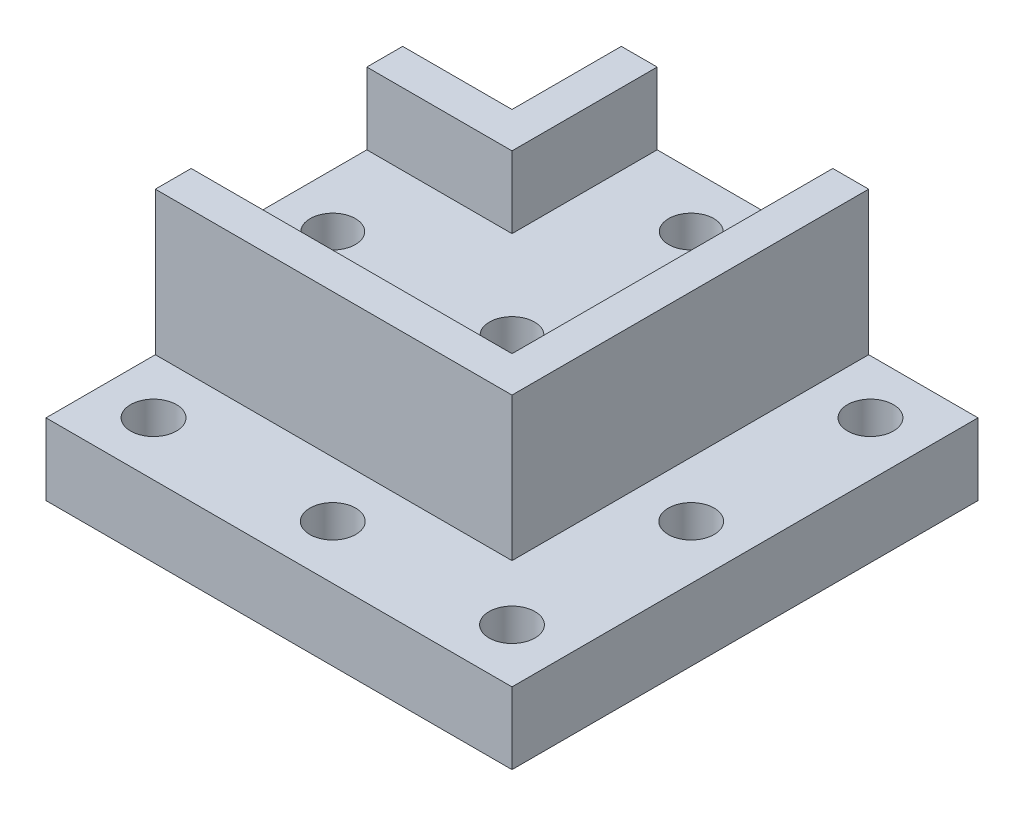
SolidWorks part; units mm, degrees
ref_plane "정면" through (0, 0, 0) normal (0, 0, 1) x (1, 0, 0)
ref_plane "윗면" through (0, 0, 0) normal (0, 1, 0) x (1, 0, 0)
ref_plane "우측면" through (0, 0, 0) normal (1, 0, 0) x (0, 0, -1)
sketch "스케치1" plane through (0, 0, 0) normal (0, 1, 0) x (1, 0, 0)
  line L1 (-32.5, 32.5) -> (32.5, 32.5)
  line L2 (-32.5, 32.5) -> (-32.5, -32.5)
  line L3 (-32.5, -32.5) -> (32.5, -32.5)
  line L4 (32.5, 32.5) -> (32.5, -32.5)
  circle A0 centre (25, 0) radius 3.2
  circle A3 centre (0, -25) radius 3.2
  circle A4 centre (25, 25) radius 3.2
  circle A5 centre (-25, 25) radius 3.2
  circle A6 centre (25, -25) radius 3.2
  circle A7 centre (-25, -25) radius 3.2
  point P6 (0, 0)
  point P7 (0, 0)
  point P8 (0, 0)
  point P9 (0, 0)
  point P20 (0, 0)
  point P21 (0, 0)
  point P22 (0, 0)
  point P24 (0, 0)
  point P25 (0, 0)
  point P26 (0, 0)
  point P27 (0, 0)
  point P28 (34.8055, 33.7643)
  point P29 (32.5, 0)
  point P30 (0, 32.5)
  point P31 (0, 0)
  point P32 (0, 0)
  point P33 (25, 25)
  point P35 (24.2327, -23.5969)
  dimension "D3" = 6.4
  dimension "D1" = 65
  dimension "D2" = 65
  dimension "D4" = 50
  dimension "D5" = 50
  dimension "D6" = 25
  dimension "D7" = 25
extrude "보스-돌출1" add sketch "스케치1" along normal blind 10
sketch "스케치2" plane through (0, 10, 0) normal (0, 1, 0) x (1, 0, 0)
  line L0 (32.5, -32.5) -> (32.5, 32.5) construction
  line L3 (-32.5, -12.25) -> (12.25, -12.25)
  line L4 (12.25, 32.5) -> (12.25, -12.25)
  line L5 (-32.5, -32.5) -> (32.5, -32.5) construction
  line L7 (-32.5, 32.5) -> (-32.5, -32.5) construction
  line L8 (32.5, 32.5) -> (-32.5, 32.5) construction
  line L12 (12.25, 32.5) -> (-12.25, 32.5)
  line L13 (-12.25, 12.25) -> (-12.25, 32.5)
  line L16 (-12.25, 12.25) -> (-32.5, 12.25)
  line L17 (-32.5, -12.25) -> (-32.5, 12.25)
  point P16 (0, 0)
  point P17 (12.25, 49.0838)
  point P18 (-54.7763, -12.25)
  dimension "D1" = 20.25
  dimension "D2" = 20.25
  dimension "D3" = 20.25
  dimension "D4" = 20.25
extrude "보스-돌출3" add sketch "스케치2" along normal blind 10
sketch "스케치4" plane through (0, 0, 0) normal (0, -1, 0) x (1, 0, 0)
  circle A0 centre (0, 0) radius 5.25
  circle A1 centre (-25, 0) radius 5.25
  circle A2 centre (0, -25) radius 5.25
  point P7 (0, 0)
  point P8 (8.0943, -23.6534)
  point P9 (0, 0)
  dimension "D3" = 10.5
  dimension "D1" = 25
  dimension "D2" = 25
extrude "컷-돌출1" cut sketch "스케치4" against normal blind 10
sketch "스케치5" plane through (0, 0, 0) normal (0, -1, 0) x (1, 0, 0)
  circle A0 centre (0, 0) radius 3.15
  circle A1 centre (0, -25) radius 3.15
  circle A2 centre (-25, 0) radius 3.15
  point P8 (0, 0)
  point P9 (0, 0)
  dimension "D2" = 6.3
  dimension "D1" = 25
extrude "컷-돌출2" cut sketch "스케치5" against normal up to surface (20 mm away) up to face at (-10.8333, 20, -10.8333)
sketch "스케치6" plane through (0, 10, 0) normal (0, 1, 0) x (1, 0, 0)
  line L0 (-12.25, 32.5) -> (-17.25, 32.5)
  line L1 (-12.25, 32.5) -> (-32.5, 32.5) construction
  line L2 (-17.25, 32.5) -> (-17.25, 17.25)
  line L3 (-17.25, 17.25) -> (-32.5, 17.25)
  line L4 (-32.5, 32.5) -> (-32.5, 12.25) construction
  line L5 (-32.5, 17.25) -> (-32.5, 12.25)
  line L6 (-32.5, 12.25) -> (-12.25, 12.25)
  line L7 (-12.25, 12.25) -> (-12.25, 32.5)
  line L8 (12.25, 32.5) -> (17.25, 32.5)
  line L9 (32.5, 32.5) -> (12.25, 32.5) construction
  line L10 (17.25, 32.5) -> (17.25, -17.25)
  line L11 (17.25, -17.25) -> (-32.5, -17.25)
  line L12 (-32.5, -12.25) -> (-32.5, -32.5) construction
  line L13 (-32.5, -17.25) -> (-32.5, -12.25)
  line L14 (-32.5, -12.25) -> (12.25, -12.25)
  line L15 (12.25, -12.25) -> (12.25, 32.5)
  dimension "D1" = 5
  dimension "D2" = 5
  dimension "D3" = 5
  dimension "D4" = 5
extrude "보스-돌출4" add sketch "스케치6" along normal blind 20
